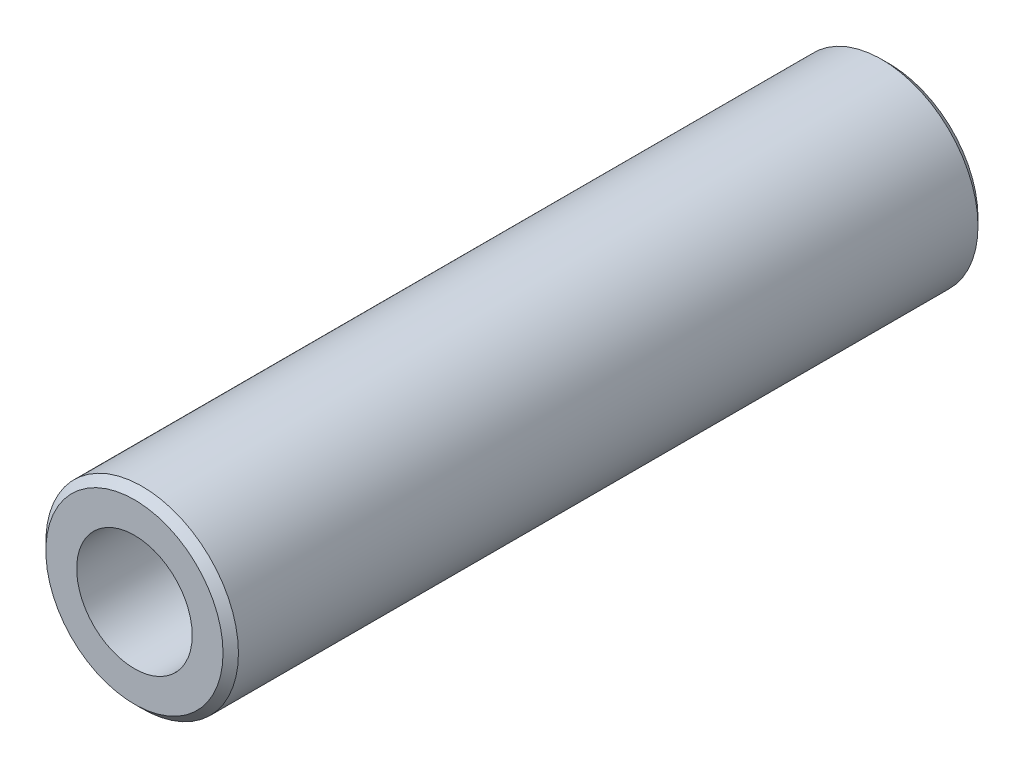
SolidWorks part; units mm, degrees
ref_plane "Front Plane" through (0, 0, 0) normal (0, 0, 1) x (1, 0, 0)
ref_plane "Top Plane" through (0, 0, 0) normal (0, 1, 0) x (1, 0, 0)
ref_plane "Right Plane" through (0, 0, 0) normal (1, 0, 0) x (0, 0, -1)
sketch "Sketch1" plane through (0, 0, 0) normal (0, 0, 1) x (1, 0, 0)
  circle A0 centre (0, 0) radius 6.25
  dimension "D1" = 12.5
extrude "Extrude-Thin1" add sketch "Sketch1" along normal mid plane 49 thin thin type one direction reverse wall 2.5
chamfer "Chamfer1" distance 0.5 angle 45 2 edges at (6.25, 0, -24.5) (6.25, 0, 24.5)
